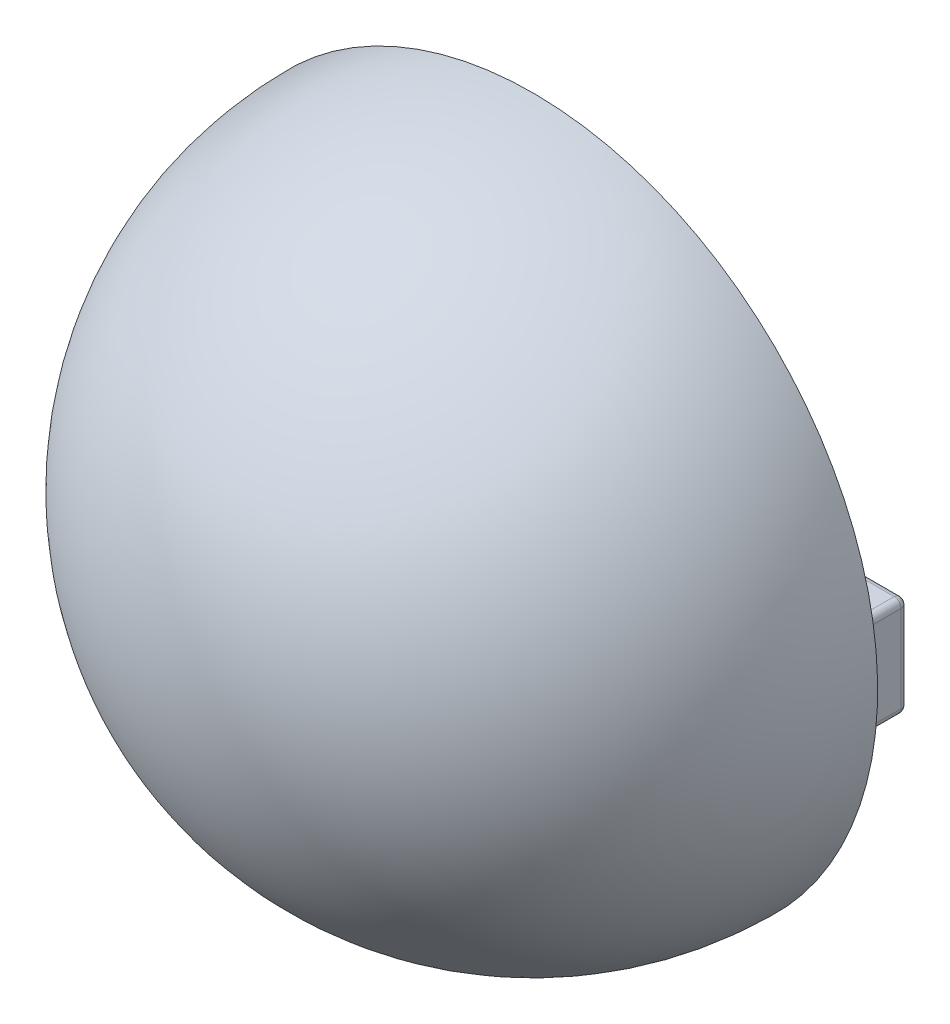
SolidWorks part; units mm, degrees
ref_plane "Plan de face" through (0, 0, 0) normal (0, 0, 1) x (1, 0, 0)
ref_plane "Plan de dessus" through (0, 0, 0) normal (0, 1, 0) x (1, 0, 0)
ref_plane "Plan de droite" through (0, 0, 0) normal (1, 0, 0) x (0, 0, -1)
sketch "Esquisse2" plane through (0, 0, 0) normal (0, 0, 1) x (1, 0, 0)
  line L0 (-41.0887, -28.4907) -> (41.0887, 28.4907) construction
  arc A0 (41.0887, 28.4907) -> (-41.0887, -28.4907) centre (0, 0) ccw
  dimension "D1" = 50
revolve "Révol.-Mince1" add sketch "Esquisse2" angle 180 about L0 wall 5
sketch "Esquisse7" plane through (0, 0, 0) normal (0, 0, 1) x (1, 0, 0)
  line L0 (-36, 27) -> (-36, 0)
  line L1 (36, -27) -> (-36, -27) construction
  line L2 (36, -27) -> (36, 27) construction
  line L3 (36, 27) -> (-36, 27) construction
  line L4 (-36, -27) -> (-36, 27) construction
  line L5 (36, -27) -> (-36, 27) construction
  line L6 (36, 27) -> (-36, -27) construction
  line L7 (-36, 0) -> (-45, 0)
  line L8 (36, 27) -> (36, 0)
  line L9 (36, 0) -> (45, 0)
  circle A0 centre (0, 0) radius 45 construction
  arc A1 (36, 27) -> (45, 0) centre (0, 0) cw
  arc A2 (-36, 27) -> (-45, 0) centre (0, 0) ccw
  point P0 (0, 0)
  point P6 (-36, 0)
  point P7 (0, 27)
  dimension "D1" = 72
revolve "Révolution1" add sketch "Esquisse7" angle 180 about L9
sketch "Esquisse8" plane through (0, 0, 0) normal (0, 0, 1) x (1, 0, 0)
  line L0 (36, 0) -> (50, 0) construction
  line L1 (47.8, 7.3) -> (38.2, 7.3)
  line L2 (47.8, 7.3) -> (47.8, -7.3)
  line L3 (47.8, -7.3) -> (38.2, -7.3)
  line L4 (38.2, 7.3) -> (38.2, -7.3)
  line L5 (47.8, 7.3) -> (38.2, -7.3) construction
  line L6 (47.8, -7.3) -> (38.2, 7.3) construction
  line L7 (36, 27) -> (36, -27) construction
  line L8 (-36, 0) -> (-50, 0) construction
  line L13 (-38.2, 7.3) -> (-47.8, 7.3)
  line L14 (-38.2, 7.3) -> (-38.2, -7.3)
  line L15 (-38.2, -7.3) -> (-47.8, -7.3)
  line L16 (-47.8, 7.3) -> (-47.8, -7.3)
  line L17 (-38.2, 7.3) -> (-47.8, -7.3) construction
  line L18 (-38.2, -7.3) -> (-47.8, 7.3) construction
  line L19 (-36, -27) -> (-36, 27) construction
  circle A0 centre (0, 0) radius 50 construction
  point P0 (43, 0)
  point P12 (43, 0)
  point P13 (43, 0)
  point P14 (-43, 0)
  point P24 (-43, 0)
  dimension "D1" = 9.6
  dimension "D2" = 14.6
  dimension "D3" = 9.6
  dimension "D4" = 14.6
extrude "Boss.-Extru.1" add sketch "Esquisse8" against normal blind 6.6
fillet "Congé1" radius 1 16 edges at (38.2, -7.3, -3.3) (38.2, 7.3, -3.3) (47.8, 7.3, -3.3) (47.8, -7.3, -3.3) (-38.2, 7.3, -3.3) (-38.2, -7.3, -3.3) (-47.8, -7.3, -3.3) (-47.8, 7.3, -3.3) (43, -7.3, -6.6) (38.2, 0, -6.6) (47.8, 0, -6.6) (43, 7.3, -6.6) (-43, -7.3, -6.6) (-38.2, 0, -6.6) (-43, 7.3, -6.6) (-47.8, 0, -6.6)
sketch "Esquisse9" plane through (0, 0, 0) normal (0, 0, 1) x (1, 0, 0)
  line L0 (36, 27) -> (-36, 27)
  line L1 (36, -27) -> (-36, -27)
  line L2 (0, 27) -> (0, 45) construction
  line L3 (0, -27) -> (0, -45) construction
  line L5 (36, 27) -> (36, -27)
  line L6 (32.5, -22.5) -> (-32.5, -22.5)
  line L7 (32.5, -22.5) -> (32.5, 22.5)
  line L8 (32.5, 22.5) -> (-32.5, 22.5)
  line L9 (-32.5, -22.5) -> (-32.5, 22.5)
  line L10 (32.5, -22.5) -> (-32.5, 22.5) construction
  line L11 (32.5, 22.5) -> (-32.5, -22.5) construction
  line L12 (-36, 27) -> (-36, -27)
  arc A0 (36, 27) -> (-36, 27) centre (0, 0) ccw construction
  arc A1 (-36, -27) -> (36, -27) centre (0, 0) ccw construction
  point P20 (0, 0)
  dimension "D1" = 65
  dimension "D2" = 45
extrude "Boss.-Extru.2" add sketch "Esquisse9" along normal blind 10
sketch "Esquisse10" plane through (0, 0, 0) normal (0, 0, -1) x (-1, 0, 0)
  line L1 (-35.5, -25.5) -> (35.5, -25.5)
  line L2 (-35.5, -25.5) -> (-35.5, 25.5)
  line L3 (-35.5, 25.5) -> (35.5, 25.5)
  line L4 (35.5, -25.5) -> (35.5, 25.5)
  line L5 (-35.5, -25.5) -> (35.5, 25.5) construction
  line L6 (-35.5, 25.5) -> (35.5, -25.5) construction
  point P0 (0, 0)
  dimension "D1" = 71
  dimension "D2" = 51
extrude "Enlèv. mat.-Extru.1" cut sketch "Esquisse10" against normal blind 5
